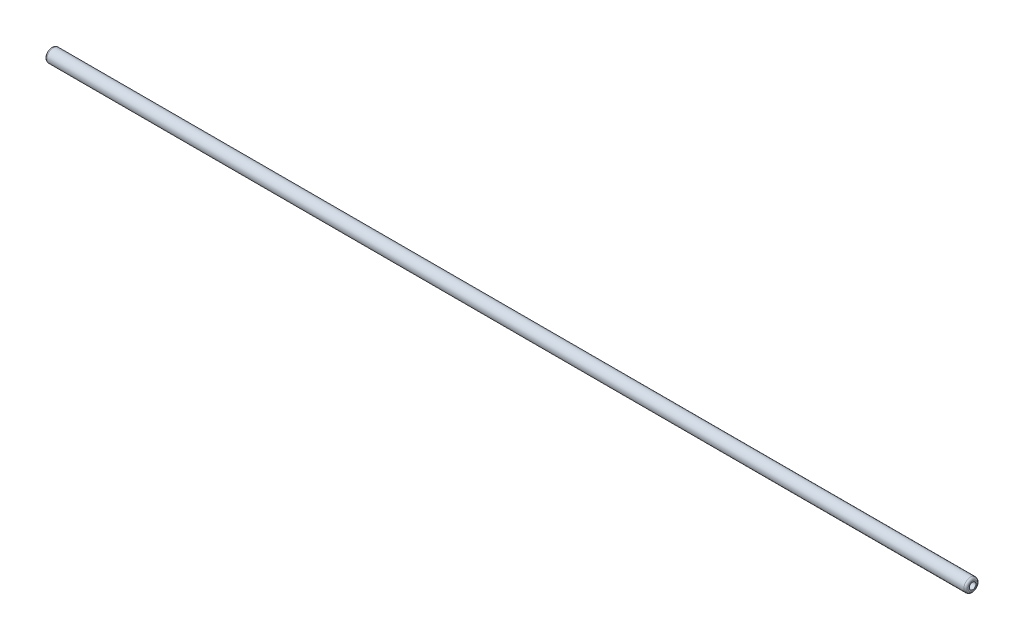
SolidWorks part; units mm, degrees
material "Alloy Steel"
ref_plane "Front Plane" through (0, 0, 0) normal (0, 0, 1) x (1, 0, 0)
ref_plane "Top Plane" through (0, 0, 0) normal (0, 1, 0) x (1, 0, 0)
ref_plane "Right Plane" through (0, 0, 0) normal (1, 0, 0) x (0, 0, -1)
sketch "스케치1" plane through (0, 0, 0) normal (0, 1, 0) x (1, 0, 0)
  circle A0 centre (0, 0) radius 7.9375
  circle A1 centre (0, 0) radius 3.975
  dimension "D1" = 15.875
  dimension "D2" = 7.95
extrude "보스-돌출1" add sketch "스케치1" along normal mid plane 1101.725
fillet "필렛1" radius 2.5 2 edges at (0, 550.8625, 7.9375) (0, -550.8625, 7.9375)
move or copy body "바디-이동/복사1" bodies to move or copy 101 copy no rotation origin (0, 0, 0) rotation axis (0, 0, 1) rotation angle 90
